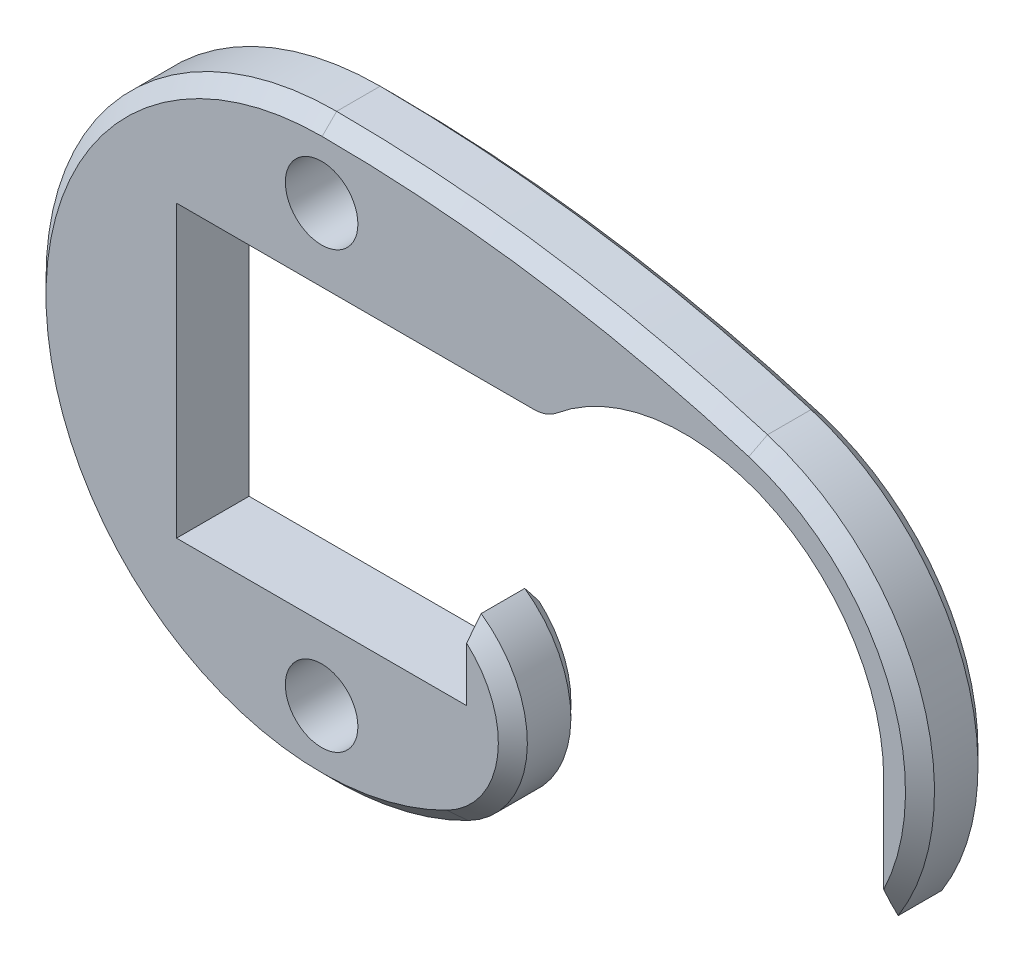
SolidWorks part; units mm, degrees
material "6061-T6 (SS)"
ref_plane "Front Plane" through (0, 0, 0) normal (0, 0, 1) x (1, 0, 0)
ref_plane "Top Plane" through (0, 0, 0) normal (0, 1, 0) x (1, 0, 0)
ref_plane "Right Plane" through (0, 0, 0) normal (1, 0, 0) x (0, 0, -1)
sketch "Sketch1" plane through (0, 0, 0) normal (0, 0, 1) x (1, 0, 0)
  line L0 (26.797, 0) -> (26.797, 51.9605) construction
  line L1 (-44.45, -12.7) -> (-19.05, -12.7) construction
  line L2 (-44.45, -12.7) -> (-44.45, 12.7) construction
  line L3 (-44.45, 12.7) -> (-19.05, 12.7) construction
  line L4 (-19.05, -12.7) -> (-19.05, 12.7) construction
  line L5 (-44.45, -12.7) -> (-19.05, 12.7) construction
  line L6 (-44.45, 12.7) -> (-19.05, -12.7) construction
  line L7 (-19.05, -12.7) -> (-44.45, -12.7)
  line L8 (-44.45, -12.7) -> (-44.45, 12.7)
  line L9 (-44.45, 12.7) -> (-11.9854, 12.7)
  line L10 (-19.05, -12.7) -> (-19.05, -6.35)
  line L11 (17.4625, -10.9985) -> (17.4625, 0)
  circle A0 centre (0, 0) radius 15.875 construction
  arc A1 (-31.7019, 25.4) -> (-20.2014, -22.6228) centre (-31.75, 0) ccw
  arc A3 (-31.7019, 25.4) -> (6.0193, 19.7402) centre (-31.9484, -104.7748) cw
  arc A4 (17.4625, 0) -> (-11.9854, 12.7) centre (0, 0) ccw
  arc A5 (-19.05, -6.35) -> (-20.2014, -22.6228) centre (-24.5321, -14.1392) cw
  arc A6 (17.4625, -10.9985) -> (6.0193, 19.7402) centre (0, 0) ccw
  point P3 (-31.75, 0)
  dimension "D1" = 31.75
  dimension "D6" = 10.9985
  dimension "D7" = 50.8
  dimension "D8" = 130.175
  dimension "D9" = 34.925
  dimension "D11" = 9.525
  dimension "D12" = 17.4625
  dimension "D2" = 25.4
  dimension "D3" = 25.4
  dimension "D4" = 45.847
  dimension "D5" = 31.75
  dimension "D10" = 6.35
  dimension "D13" = 19.7402
extrude "Boss-Extrude1" add sketch "Sketch1" along normal mid plane 6.35
fillet "Fillet1" radius 3.175 1 edges at (-11.9854, 12.7, 0)
sketch "Sketch2" plane through (0, 0, 3.175) normal (0, 0, 1) x (1, 0, 0)
  line L0 (-31.75, -12.7) -> (-31.75, -25.4) construction
  line L1 (-19.05, -12.7) -> (-44.45, -12.7) construction
  line L2 (0, 0) -> (-44.45, 0) construction
  line L3 (-44.45, -12.7) -> (-44.45, 12.7) construction
  circle A0 centre (-31.75, -19.05) radius 3.175
  arc A1 (-31.7019, 25.4) -> (-20.2014, -22.6228) centre (-31.75, 0) ccw construction
  circle A2 centre (-31.75, 19.05) radius 3.175
  point P11 (-31.75, -19.05)
  dimension "D1" = 6.35
extrude "Cut-Extrude1" cut sketch "Sketch2" against normal through all both and the other way through all
chamfer "Chamfer1" distance 1.27 angle 45 8 edges at (-15.0309, -14.8115, -3.175) (-56.4515, -5.9155, -3.175) (-12.6329, 23.9592, -3.175) (19.3408, 7.2001, -3.175) (19.3408, 7.2001, 3.175) (-15.0309, -14.8115, 3.175) (-56.4515, -5.9155, 3.175) (-12.6329, 23.9592, 3.175)
